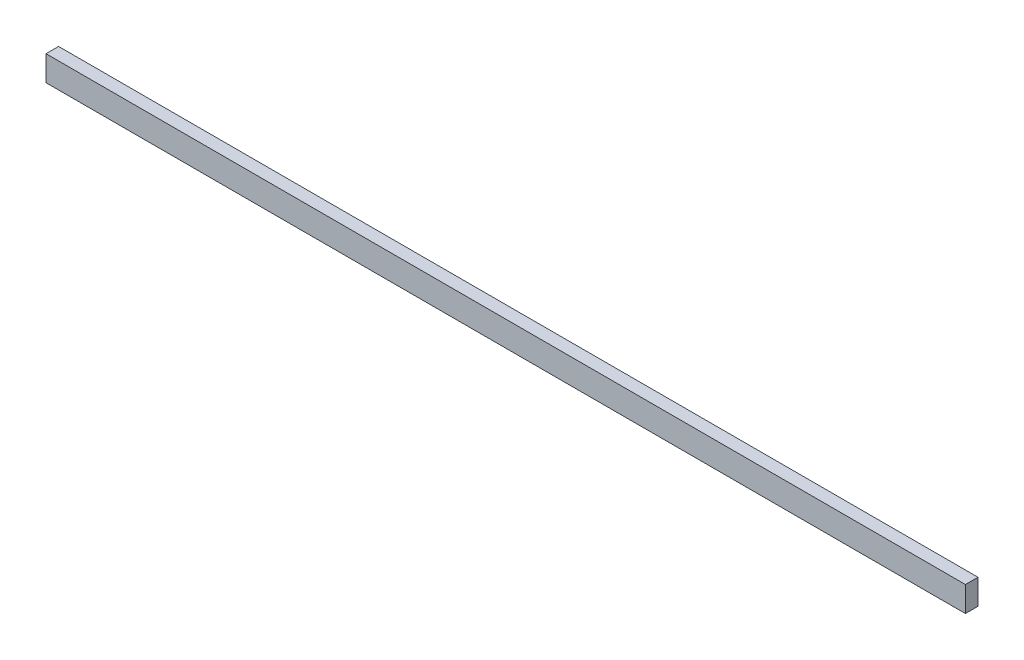
SolidWorks part; units mm, degrees
material "Erable"
ref_plane "Plan de face" through (0, 0, 0) normal (0, 0, 1) x (1, 0, 0)
ref_plane "Plan de dessus" through (0, 0, 0) normal (0, 1, 0) x (1, 0, 0)
ref_plane "Plan de droite" through (0, 0, 0) normal (1, 0, 0) x (0, 0, -1)
sketch "Esquisse1" plane through (0, 0, 0) normal (0, 0, 1) x (1, 0, 0)
  line L1 (-548, 15) -> (548, 15)
  line L2 (-548, 15) -> (-548, -15)
  line L3 (-548, -15) -> (548, -15)
  line L4 (548, 15) -> (548, -15)
  line L5 (-548, 15) -> (548, -15) construction
  line L6 (-548, -15) -> (548, 15) construction
  point P0 (0, 0)
  dimension "D1" = 1096
  dimension "D2" = 30
extrude "Boss.-Extru.1" add sketch "Esquisse1" along normal blind 15
